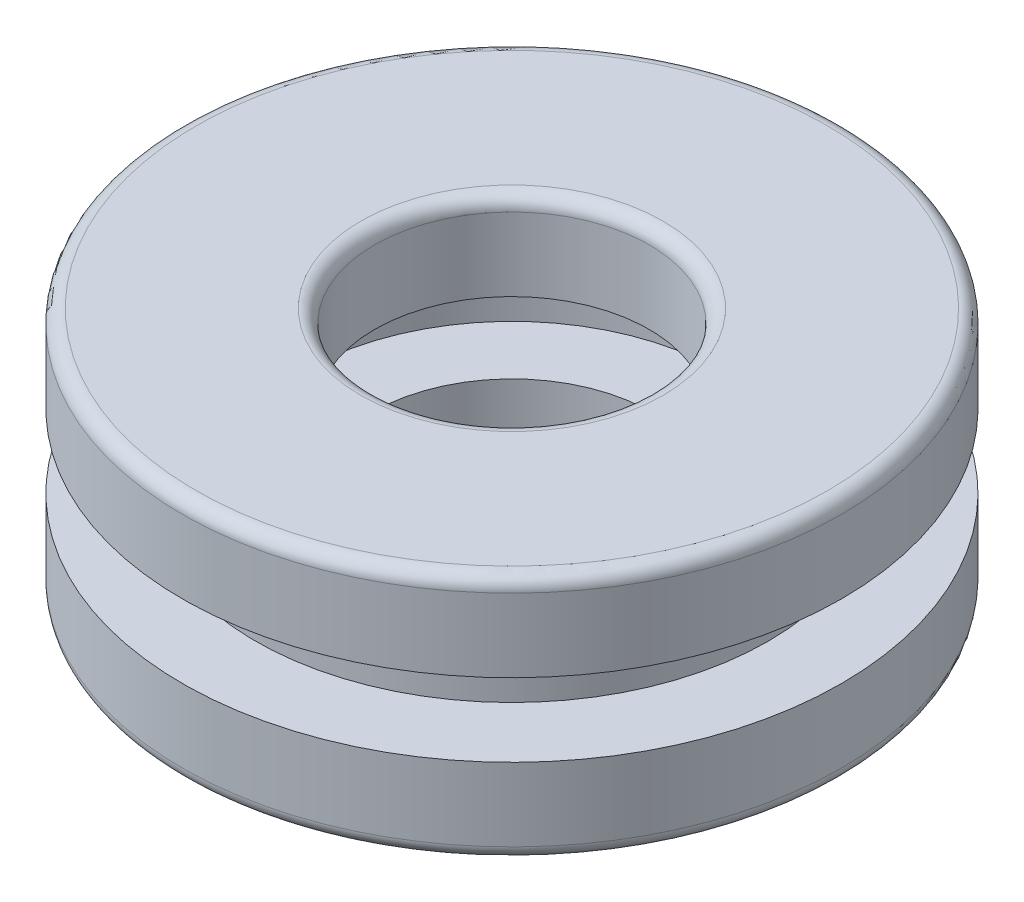
SolidWorks part; units mm, degrees
material "AISI 1020"
ref_plane "Спереди" through (0, 0, 0) normal (0, 0, 1) x (1, 0, 0)
ref_plane "Сверху" through (0, 0, 0) normal (0, 1, 0) x (1, 0, 0)
ref_plane "Справа" through (0, 0, 0) normal (1, 0, 0) x (0, 0, -1)
sketch "Эскиз1" plane through (0, 0, 0) normal (0, 0, 1) x (1, 0, 0)
  line L0 (0, -1000) -> (0, 49000) construction
  line L2 (5.1, 3.1667) -> (7.6667, 3.1667)
  line L3 (5.1, 3.1667) -> (5.1, 0.5)
  line L4 (5.6, 0) -> (11.5, 0)
  line L5 (12, 3.1667) -> (12, 0.5)
  line L7 (5.5, 9) -> (11.5, 9)
  line L8 (5, 8.5) -> (5, 5.8333)
  line L9 (5, 5.8333) -> (7.6667, 5.8333)
  line L10 (12, 8.5) -> (12, 5.8333)
  line L13 (7.6667, 5.8333) -> (7.6667, 3.1667)
  line L15 (9.3333, 5.8333) -> (9.3333, 3.1667)
  line L16 (9.3333, 5.8333) -> (12, 5.8333)
  line L17 (9.3333, 3.1667) -> (12, 3.1667)
  arc A0 (5.1, 0.5) -> (5.6, 0) centre (5.6, 0.5) ccw
  arc A1 (11.5, 0) -> (12, 0.5) centre (11.5, 0.5) ccw
  arc A2 (11.5, 9) -> (12, 8.5) centre (11.5, 8.5) cw
  arc A3 (5.5, 9) -> (5, 8.5) centre (5.5, 8.5) ccw
  point P11 (12, 7.1667)
  dimension "D2" = 0.5
  dimension "_D" = 24
  dimension "_d1_" = 24
  dimension "_d_" = 10
  dimension "_D1" = 10.2
  dimension "_H" = 9
revolve "Повернуть1" add sketch "Эскиз1" angle 360 about L0
equation "\"_d1_@Эскиз1\"=\"_D@Эскиз1\""
